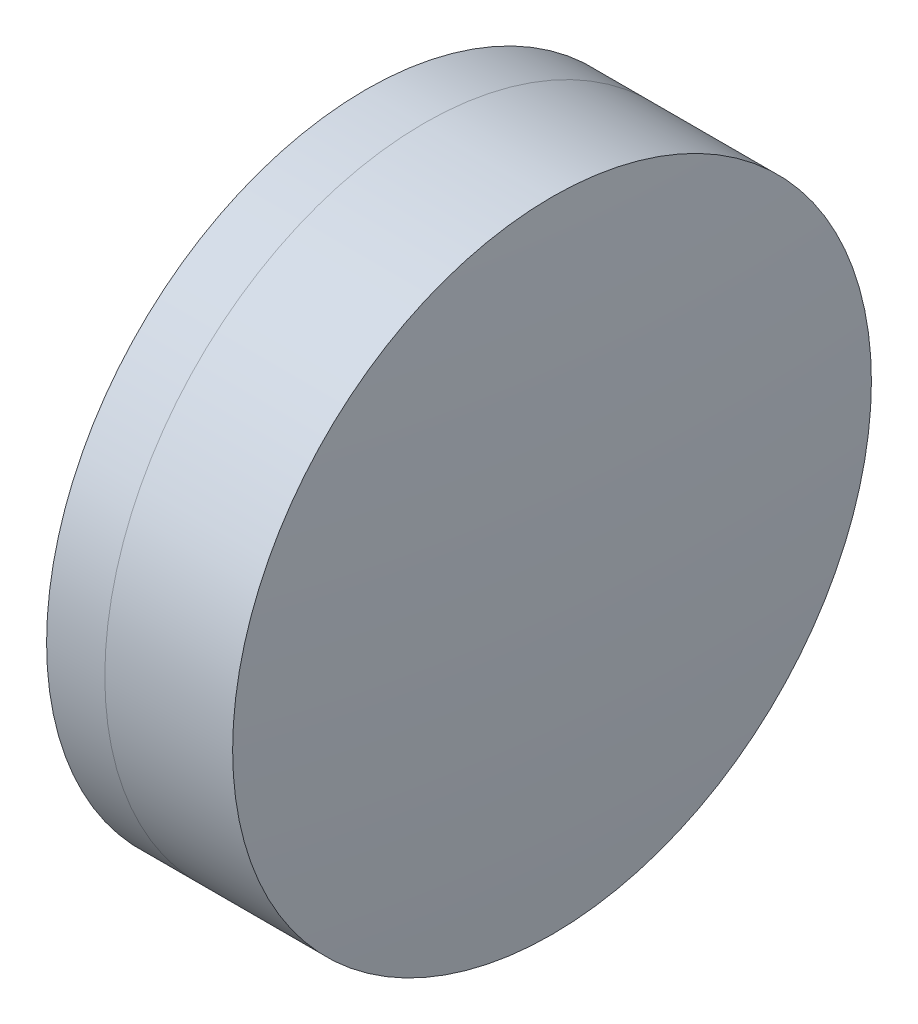
SolidWorks part; units mm, degrees
ref_plane "前视基准面" through (0, 0, 0) normal (0, 0, 1) x (1, 0, 0)
ref_plane "上视基准面" through (0, 0, 0) normal (0, 1, 0) x (1, 0, 0)
ref_plane "右视基准面" through (0, 0, 0) normal (1, 0, 0) x (0, 0, -1)
sketch "草图1" plane through (0, 0, 0) normal (0, 1, 0) x (1, 0, 0)
  line L0 (124.5233, 0) -> (646.9917, 0) construction
  line L1 (274.4548, -6.35) -> (275.6126, -6.35)
  line L2 (274.4548, 6.35) -> (275.6126, 6.35)
  arc A0 (275.6126, -6.35) -> (275.6126, 6.35) centre (260.709, 0) ccw
  arc A1 (274.4548, 6.35) -> (274.4548, -6.35) centre (293.209, 0) ccw
  point P10 (273.409, 0)
  point P11 (276.909, 0)
  dimension "D3" = 19.8
  dimension "D4" = 16.2
  dimension "D1" = 6.35
  dimension "D2" = 6.35
  dimension "D5" = 3.5
revolve "旋转1" add sketch "草图1" angle 360 about L0
sketch "草图2" plane through (0, 0, 0) normal (0, 1, 0) x (1, 0, 0)
  line L0 (-0.5519, 0) -> (622.6607, 0) construction
  line L2 (275.6126, 6.35) -> (278.1537, 6.35)
  line L3 (275.6126, -6.35) -> (278.1537, -6.35)
  arc A0 (278.1537, -6.35) -> (278.1537, 6.35) centre (199.309, 0) ccw
  arc A1 (275.6126, -6.35) -> (275.6126, 6.35) centre (260.709, 0) ccw construction
  arc A2 (275.6126, -6.35) -> (275.6126, 6.35) centre (260.709, 0) ccw
  point P4 (276.909, 0)
  point P8 (278.409, 0)
  dimension "D1" = 79.1
  dimension "D2" = 1.5
revolve "旋转3" add sketch "草图2" angle 360 about L0
